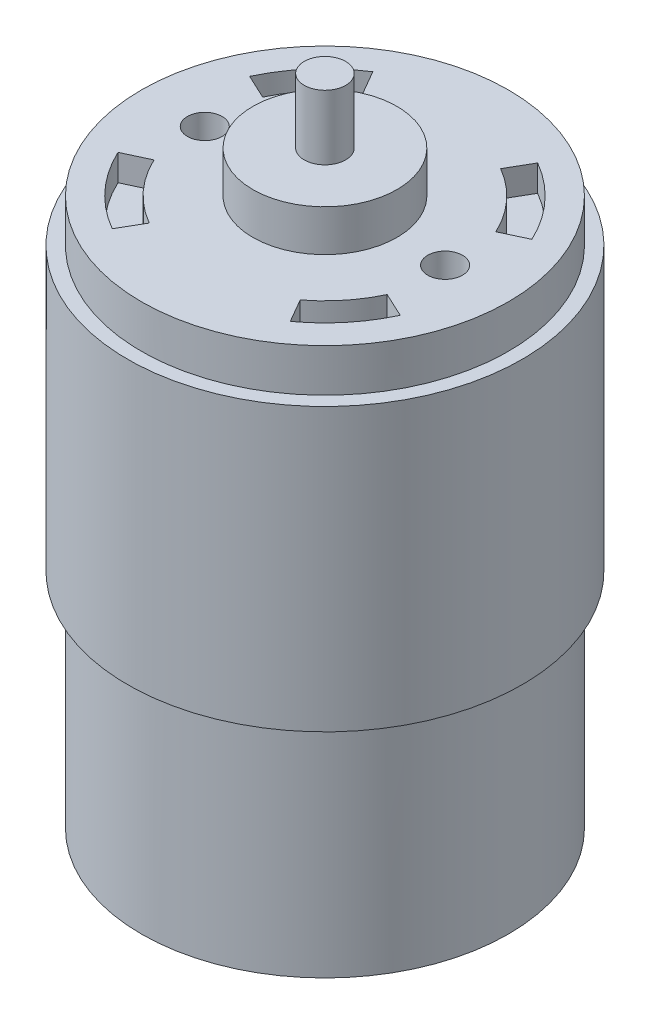
SolidWorks part; units mm, degrees
ref_plane "Front Plane" through (0, 0, 0) normal (0, 0, 1) x (1, 0, 0)
ref_plane "Top Plane" through (0, 0, 0) normal (0, 1, 0) x (1, 0, 0)
ref_plane "Right Plane" through (0, 0, 0) normal (1, 0, 0) x (0, 0, -1)
sketch "Sketch2" plane through (0, 0, 0) normal (0, 1, 0) x (1, 0, 0)
  circle A0 centre (0, 0) radius 22.1488
  dimension "D1" = 44.2976
extrude "Boss-Extrude4" add sketch "Sketch2" along normal blind 66.0908
sketch "Sketch4" plane through (0, 66.0908, 0) normal (0, 1, 0) x (1, 0, 0)
  circle A0 centre (0, 0) radius 8.6995
  dimension "D1" = 17.399
extrude "Boss-Extrude5" add sketch "Sketch4" along normal blind 5.0038 contours A0
sketch "Sketch9" plane through (0, 71.0946, 0) normal (0, 1, 0) x (1, 0, 0)
  circle A0 centre (0, 0) radius 2.5019
  dimension "D1" = 5.0038
extrude "Boss-Extrude6" add sketch "Sketch9" along normal blind 7.7978
sketch "Sketch10" plane through (0, 0, 0) normal (0, -1, 0) x (1, 0, 0)
  circle A0 centre (0, 0) radius 8.7503
  dimension "D1" = 17.5006
extrude "Boss-Extrude7" add sketch "Sketch10" along normal blind 6.7056
sketch "Sketch11" plane through (0, -6.7056, 0) normal (0, -1, 0) x (1, 0, 0)
  circle A0 centre (0, 0) radius 2.5019
  dimension "D1" = 5.0038
extrude "Boss-Extrude8" add sketch "Sketch11" along normal blind 2.413
ref_plane "Plane2" through (0, 60.9092, 0) normal (0, -1, 0) x (-1, 0, 0)
sketch "Sketch12" plane through (0, 60.9092, 0) normal (0, -1, 0) x (-1, 0, 0)
  circle A0 centre (0, 0) radius 23.8125
  dimension "D1" = 47.625
extrude "Boss-Extrude9" add sketch "Sketch12" along normal blind 34.0106
sketch "Sketch13" plane through (0, 66.0908, 0) normal (0, 1, 0) x (1, 0, 0)
  line L0 (-29.6451, 0) -> (29.6451, 0) construction
  line L1 (0, -27.354) -> (0, 29.9922) construction
  circle A0 centre (-14.5034, 0) radius 2.0955
  circle A1 centre (0, 0) radius 14.5034 construction
  circle A2 centre (14.5034, 0) radius 2.0955
  dimension "D1" = 4.191
  dimension "D2" = 29.0068
extrude "Cut-Extrude1" cut sketch "Sketch13" against normal blind 3.175
sketch "Sketch14" plane through (0, 66.0908, 0) normal (0, 1, 0) x (1, 0, 0)
  line L0 (-17.0333, -7.9428) -> (-14.07, -6.561)
  line L1 (-9.3971, -16.2762) -> (-7.7623, -13.4446)
  line L2 (-24.8296, 0) -> (26.0831, 0) construction
  line L3 (0, -32.9776) -> (0, 32.0133) construction
  line L4 (-17.0333, 7.9428) -> (-14.07, 6.561)
  line L5 (-10.0803, 15.8622) -> (-8.4437, 13.0275)
  line L6 (7.7623, 13.4446) -> (9.3971, 16.2762)
  line L7 (14.07, 6.561) -> (17.0333, 7.9428)
  line L8 (9.3859, -12.3659) -> (11.0315, -15.216)
  line L9 (14.07, -6.561) -> (17.0333, -7.9428)
  circle A0 centre (0, 0) radius 16.306 construction
  circle A1 centre (0, 0) radius 18.7942
  circle A2 centre (0, 0) radius 15.5245
  dimension "D1" = 65
  dimension "D2" = 30
  dimension "D3" = 30
  dimension "D4" = 65
  dimension "D5" = 30
  dimension "D6" = 65
  dimension "D7" = 65
  dimension "D8" = 30
extrude "Cut-Extrude2" cut sketch "Sketch14" against normal blind 3.175 contours A2 L0 A1 L1 | A2 L5 A1 L4 | A2 L7 A1 L6 | A2 L8 A1 L9
sketch "Sketch15" plane through (0, 0, 0) normal (0, -1, 0) x (1, 0, 0)
  circle A0 centre (0, 0) radius 8.7503
  circle A1 centre (0, 0) radius 20.9582
  circle A2 centre (0, 0) radius 22.1488 construction
  dimension "D1" = 1.1906
extrude "Cut-Extrude3" cut sketch "Sketch15" against normal blind 3.175
sketch "Sketch16" plane through (0, -6.7056, 0) normal (0, -1, 0) x (1, 0, 0)
  circle A0 centre (0, 0) radius 2.5019
  circle A1 centre (0, 0) radius 7.1628
  circle A2 centre (0, 0) radius 8.7503 construction
  dimension "D1" = 1.5875
extrude "Cut-Extrude4" cut sketch "Sketch16" against normal blind 2.54
sketch "Sketch18" plane through (0, 0, 0) normal (0, -1, 0) x (1, 0, 0)
  line L1 (20.5261, 3.7465) -> (17.399, 3.7465)
  line L3 (20.7021, -2.6035) -> (17.399, -2.6035)
  line L4 (17.399, 3.7465) -> (17.399, -2.6035)
  circle A0 centre (0, 0) radius 20.8652
  dimension "D1" = 17.399
  dimension "D2" = 6.35
extrude "Boss-Extrude12" add sketch "Sketch18" against normal blind 3.175 contours L3 A0 L1 L4
sketch "Sketch19" plane through (0, 0, 0) normal (0, -1, 0) x (-1, 0, 0)
  line L1 (20.7163, -3.175) -> (17.399, -3.175)
  line L3 (20.7163, 3.175) -> (17.399, 3.175)
  line L4 (17.399, -3.175) -> (17.399, 3.175)
  circle A0 centre (0, 0) radius 20.9582 construction
  arc A1 (20.7163, -3.175) -> (20.7163, 3.175) centre (0, 0) ccw
  dimension "D1" = 6.35
  dimension "D2" = 17.399
extrude "Boss-Extrude13" add sketch "Sketch19" against normal blind 3.175
sketch "Sketch20" plane through (0, 3.175, 0) normal (0, -1, 0) x (-1, 0, 0)
  circle A0 centre (-15.1765, 6.731) radius 1.5875
  dimension "D1" = 3.175
  dimension "D2" = 4.1275
  dimension "D3" = 2.2225
extrude "Cut-Extrude5" cut sketch "Sketch20" against normal blind 3.175
